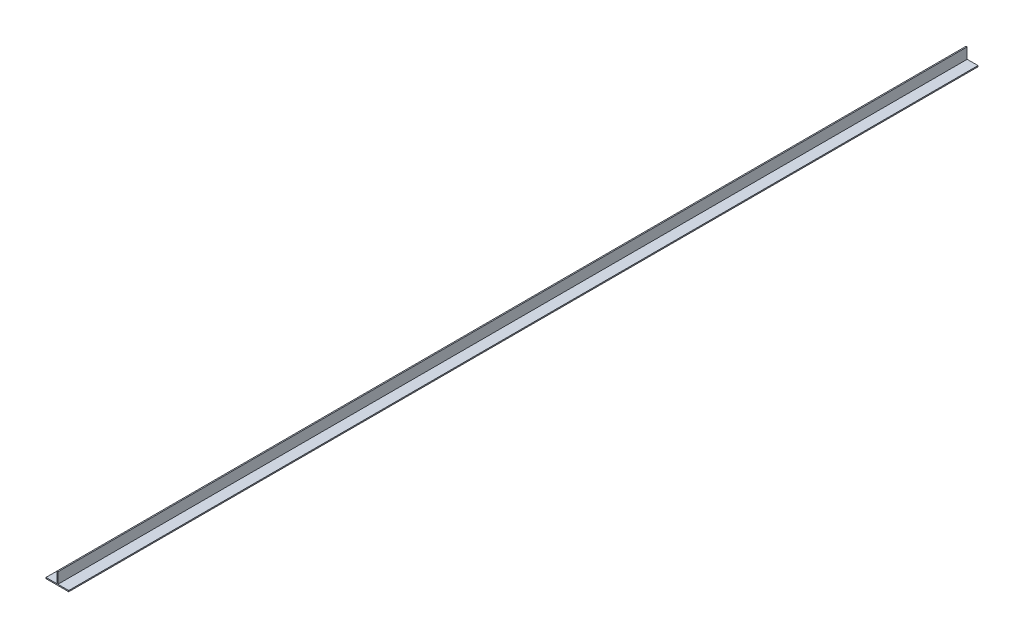
SolidWorks part; units mm, degrees
ref_plane "Alzado" through (0, 0, 0) normal (0, 0, 1) x (1, 0, 0)
ref_plane "Planta" through (0, 0, 0) normal (0, 1, 0) x (1, 0, 0)
ref_plane "Vista lateral" through (0, 0, 0) normal (1, 0, 0) x (0, 0, -1)
sketch "Croquis1" plane through (0, 0, 0) normal (0, 0, 1) x (1, 0, 0)
  line L0 (0, 5.0109) -> (0, -1.6999) construction
  line L1 (-10, 0) -> (-0.5, 0)
  line L2 (-10, 0) -> (-10, -1)
  line L3 (-10, -1) -> (10, -1)
  line L4 (10, 0) -> (10, -1)
  line L5 (-10, 0) -> (10, -1) construction
  line L6 (-10, -1) -> (10, 0) construction
  line L8 (-0.5, 0) -> (-0.5, 9.5)
  line L9 (-0.5, 9.5) -> (0.5, 9.5)
  line L10 (0.5, 0) -> (0.5, 9.5)
  line L11 (0.5, 0) -> (10, 0)
  line L12 (2.26, 0) -> (-2.189, 0) construction
  point P0 (0, -0.5)
  point P12 (0, 9.5)
  dimension "D1" = 1
  dimension "D2" = 1
  dimension "D3" = 20
  dimension "D4" = 9.5
  dimension "D5" = 9.5
extrude "Saliente-Extruir1" add sketch "Croquis1" along normal mid plane 800
